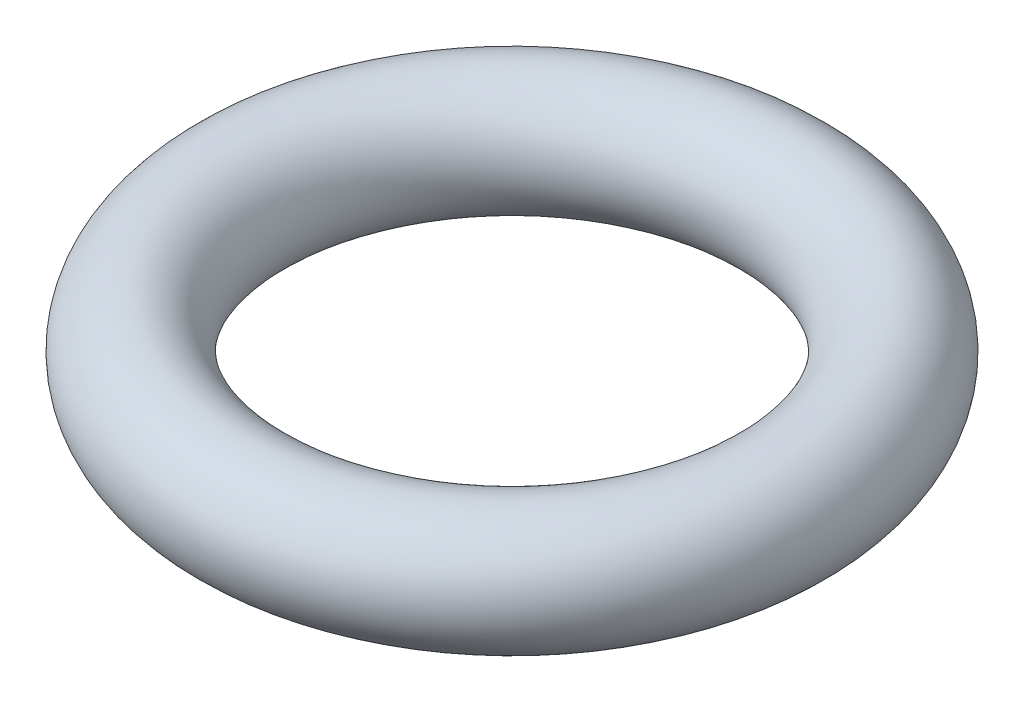
SolidWorks part; units mm, degrees
ref_plane "Front Plane" through (0, 0, 0) normal (0, 0, 1) x (1, 0, 0)
ref_plane "Top Plane" through (0, 0, 0) normal (0, 1, 0) x (1, 0, 0)
ref_plane "Right Plane" through (0, 0, 0) normal (1, 0, 0) x (0, 0, -1)
sketch "Sketch1" plane through (0, 0, 0) normal (0, 0, 1) x (1, 0, 0)
  line L0 (0, 0) -> (0, 12.7324) construction
  circle A0 centre (-4.5, 0) radius 1
  dimension "D1" = 2
  dimension "D2" = 3.5
revolve "Revolve1" add sketch "Sketch1" angle 360 about L0
sketch "Sketch2" plane through (0, 0, 0) normal (0, 1, 0) x (1, 0, 0)
  circle A0 centre (0, 0) radius 2.5 construction
  dimension "D1" = 5
equation "\"Ø_cross_section\"= 2"
equation "\"D1@Sketch1\"=\"Ø_cross_section\""
equation "\"Ø_inside\"= 6"
equation "\"D2@Sketch1\"=\"Ø_inside\"/2"
